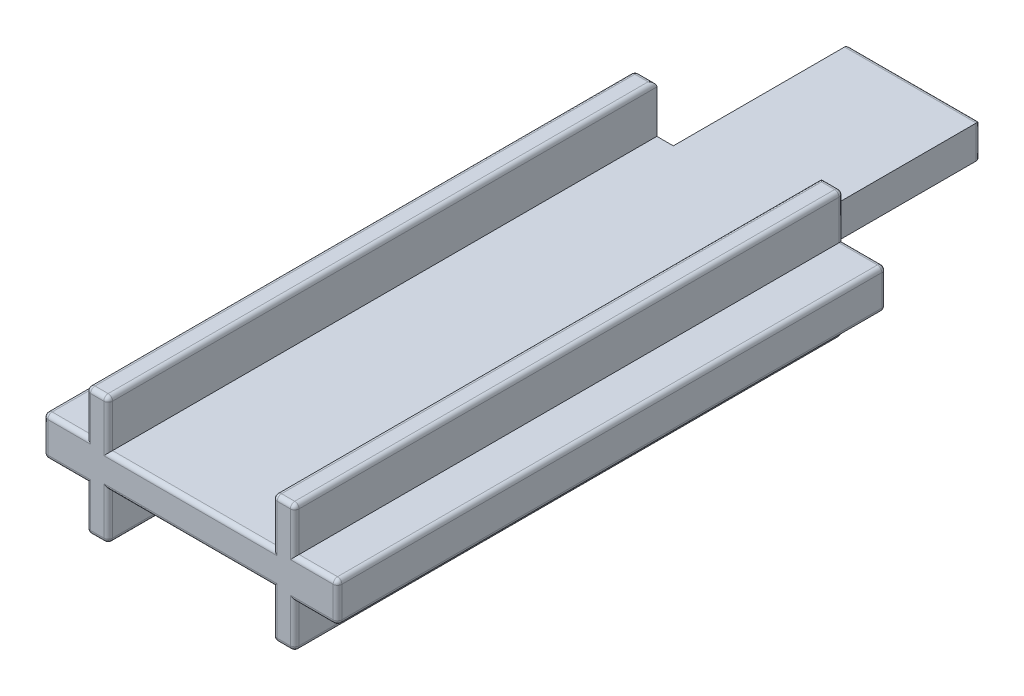
SolidWorks part; units mm, degrees
ref_plane "Ebene vorne" through (0, 0, 0) normal (0, 0, 1) x (1, 0, 0)
ref_plane "Ebene oben" through (0, 0, 0) normal (0, 1, 0) x (1, 0, 0)
ref_plane "Ebene rechts" through (0, 0, 0) normal (1, 0, 0) x (0, 0, -1)
sketch "Skizze1" plane through (0, 0, 0) normal (0, 0, 1) x (1, 0, 0)
  line L0 (-4.75, 0.9) -> (-6.7, 0.9)
  line L1 (6.7, -0.9) -> (4.75, -0.9)
  line L2 (6.7, -0.9) -> (6.7, 0.9)
  line L3 (6.7, 0.9) -> (4.75, 0.9)
  line L4 (-6.7, -0.9) -> (-6.7, 0.9)
  line L5 (6.7, -0.9) -> (-6.7, 0.9) construction
  line L6 (6.7, 0.9) -> (-6.7, -0.9) construction
  line L7 (-4.75, -2.9) -> (-3.75, -2.9)
  line L8 (-4.75, -2.9) -> (-4.75, -0.9)
  line L9 (-4.75, 2.9) -> (-3.75, 2.9)
  line L10 (-3.75, -2.9) -> (-3.75, -0.9)
  line L11 (-4.75, -2.9) -> (-3.75, 2.9) construction
  line L12 (-4.75, 2.9) -> (-3.75, -2.9) construction
  line L13 (4.75, -2.9) -> (3.75, -2.9)
  line L14 (4.75, -2.9) -> (4.75, -0.9)
  line L15 (4.75, 2.9) -> (3.75, 2.9)
  line L16 (3.75, -2.9) -> (3.75, -0.9)
  line L17 (4.75, -2.9) -> (3.75, 2.9) construction
  line L18 (4.75, 2.9) -> (3.75, -2.9) construction
  line L19 (-4.75, -0.9) -> (-6.7, -0.9)
  line L20 (-4.75, 0.9) -> (-4.75, 2.9)
  line L21 (-3.75, 0.9) -> (-3.75, 2.9)
  line L22 (3.75, -0.9) -> (-3.75, -0.9)
  line L23 (3.75, 0.9) -> (3.75, 2.9)
  line L24 (4.75, 0.9) -> (4.75, 2.9)
  line L25 (3.75, 0.9) -> (-3.75, 0.9)
  point P0 (0, 0)
  point P5 (-4.25, 0)
  point P11 (4.25, 0)
  dimension "D1" = 1.8
  dimension "D2" = 5.8
  dimension "D3" = 13.4
  dimension "D4" = 9.5
  dimension "D5" = 1
  dimension "D6" = 4.75
extrude "Aufsatz-Linear austragen1" add sketch "Skizze1" along normal blind 25
sketch "Skizze2" plane through (0, 0, 0) normal (0, 0, -1) x (-1, 0, 0)
  line L0 (-3.75, 0.9) -> (3.75, 0.9) construction
  line L1 (3, -0.9) -> (-3, -0.9)
  line L2 (3, -0.9) -> (3, 0.9)
  line L3 (3, 0.9) -> (-3, 0.9)
  line L4 (-3, -0.9) -> (-3, 0.9)
  line L5 (3, -0.9) -> (-3, 0.9) construction
  line L6 (3, 0.9) -> (-3, -0.9) construction
  point P0 (0, 0)
  dimension "D1" = 6
extrude "Aufsatz-Linear austragen2" add sketch "Skizze2" along normal blind 8
sketch "Skizze3" plane through (0, 0, 25) normal (0, 0, 1) x (1, 0, 0)
  line L1 (-3.75, -0.9) -> (3.75, -0.9)
  line L2 (-3.75, -0.9) -> (-3.75, -0.75)
  line L3 (-3.75, -0.75) -> (3.75, -0.75)
  line L4 (3.75, -0.9) -> (3.75, -0.75)
  line L5 (3.75, 0.9) -> (-3.75, 0.9)
  line L6 (3.75, 0.9) -> (3.75, 0.75)
  line L7 (3.75, 0.75) -> (-3.75, 0.75)
  line L8 (-3.75, 0.9) -> (-3.75, 0.75)
  dimension "D1" = 1.5
  dimension "D2" = 0.75
extrude "Schnitt-Linear austragen1" cut sketch "Skizze3" against normal through all
fillet "Verrundung1" radius 0.2 50 edges at (-5.725, 0.9, 25) (-4.75, 1.9, 25) (-3.75, 1.825, 25) (3.75, 1.825, 25) (4.75, 1.9, 25) (5.725, 0.9, 25) (5.725, -0.9, 25) (4.75, -1.9, 25) (3.75, -1.825, 25) (-3.75, -1.825, 25) (-4.75, -1.9, 25) (-5.725, -0.9, 25) (-3, 0, -8) (3, 0, -8) (-6.7, 0.9, 12.5) (-6.7, 0, 25) (-6.7, -0.9, 12.5) (-6.7, 0, 0) (6.7, -0.9, 12.5) (6.7, 0, 25) (6.7, 0.9, 12.5) (6.7, 0, 0) (-4.75, -2.9, 12.5) (-3.75, -2.9, 12.5) (-4.25, -2.9, 0) (3.75, -2.9, 12.5) (4.75, -2.9, 12.5) (4.25, -2.9, 0) (-3.75, 2.9, 12.5) (-4.75, 2.9, 12.5) (-4.25, 2.9, 0) (4.75, 2.9, 12.5) (3.75, 2.9, 12.5) (4.25, 2.9, 0) (4.75, 1.9, 0) (5.725, 0.9, 0) (5.725, -0.9, 0) (4.75, -1.9, 0) (-4.75, 1.9, 0) (-4.75, -1.9, 0) (-5.725, 0.9, 0) (-5.725, -0.9, 0) (-4.25, -2.9, 25) (4.25, -2.9, 25) (-4.25, 2.9, 25) (4.25, 2.9, 25) (0, 0.75, 25) (0, -0.75, 25) (0, 0.75, -8) (0, -0.75, -8)
